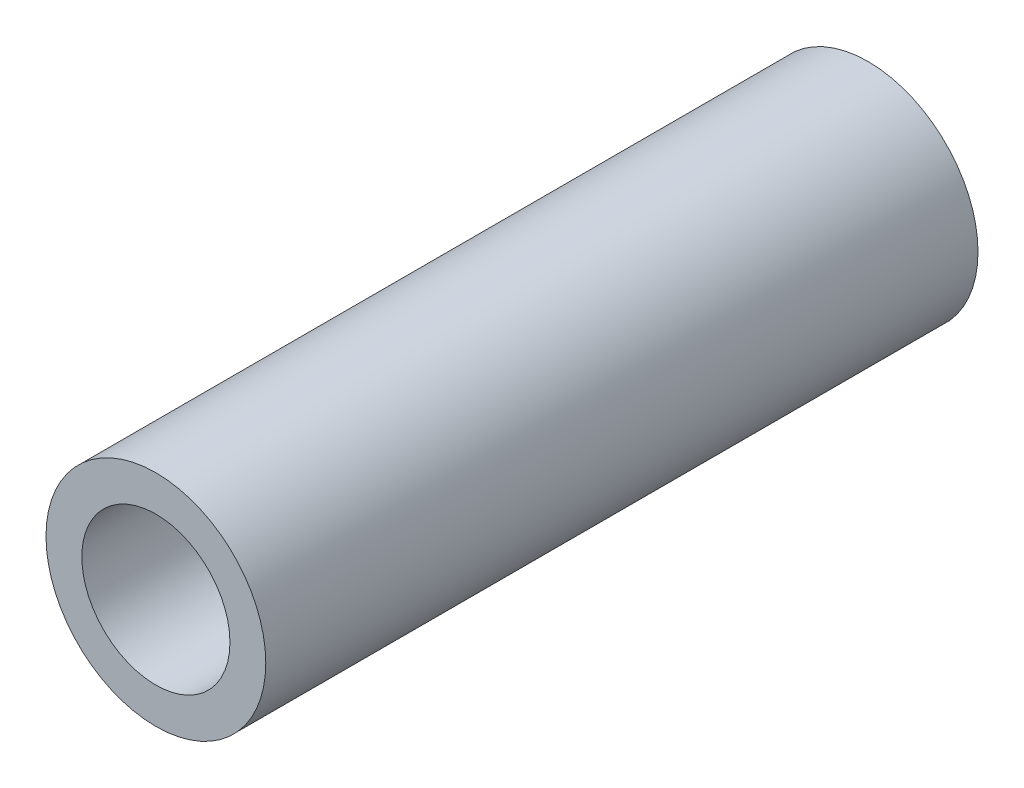
SolidWorks part; units mm, degrees
material "Plain Carbon Steel"
ref_plane "Front Plane" through (0, 0, 0) normal (0, 0, 1) x (1, 0, 0)
ref_plane "Top Plane" through (0, 0, 0) normal (0, 1, 0) x (1, 0, 0)
ref_plane "Right Plane" through (0, 0, 0) normal (1, 0, 0) x (0, 0, -1)
sketch "Sketch1" plane through (0, 0, 0) normal (0, 0, 1) x (1, 0, 0)
  line L0 (-4.6228, 0) -> (-6.858, 0) construction
  circle A0 centre (0, 0) radius 6.858
  circle A1 centre (0, 0) radius 4.6228
  dimension "OD" = 13.716
  dimension "ID" = 9.2456
extrude "Extrude1" add sketch "Sketch1" along normal mid plane 44.45
